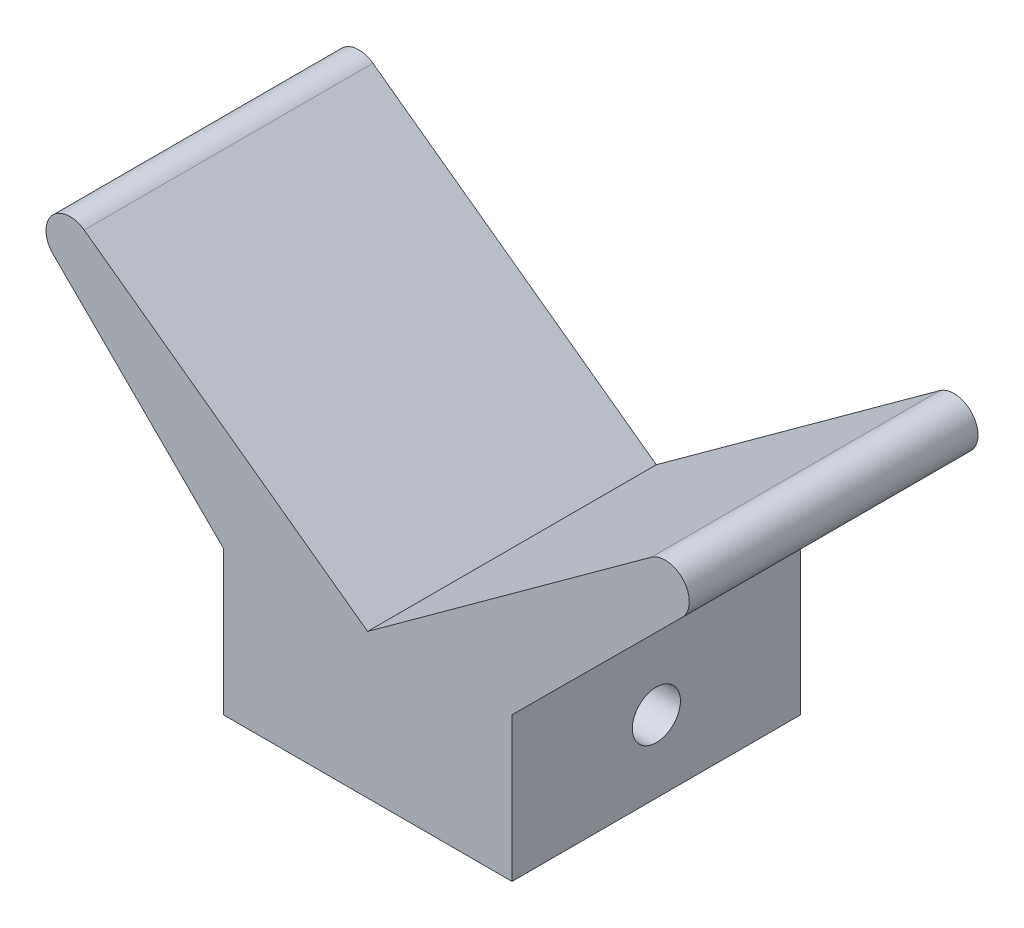
SolidWorks part; units mm, degrees
ref_plane "Front Plane" through (0, 0, 0) normal (0, 0, 1) x (1, 0, 0)
ref_plane "Top Plane" through (0, 0, 0) normal (0, 1, 0) x (1, 0, 0)
ref_plane "Right Plane" through (0, 0, 0) normal (1, 0, 0) x (0, 0, -1)
sketch "Sketch1" plane through (0, 0, 0) normal (0, 0, 1) x (1, 0, 0)
  line L0 (-38.1, 0) -> (38.1, 0)
  line L1 (38.1, 0) -> (38.1, 38.1)
  line L2 (38.1, 38.1) -> (83.0182, 82.8121)
  line L3 (74.806, 92.4498) -> (0, 38.1)
  line L4 (0, 0) -> (0, 38.1) construction
  line L5 (-74.806, 92.4498) -> (0, 38.1)
  line L6 (-38.1, 38.1) -> (-83.0182, 82.8121)
  line L7 (-38.1, 0) -> (-38.1, 38.1)
  arc A0 (83.0182, 82.8121) -> (74.806, 92.4498) centre (78.5385, 87.3125) ccw
  arc A1 (-83.0182, 82.8121) -> (-74.806, 92.4498) centre (-78.5385, 87.3125) cw
  point P13 (0, 0)
  point P14 (0, 0)
  dimension "D1" = 76.2
  dimension "D5" = 6.35
  dimension "D2" = 38.1
  dimension "D3" = 87.3125
  dimension "D4" = 108
extrude "Boss-Extrude1" add sketch "Sketch1" along normal blind 76.2
sketch "Sketch2" plane through (38.1, 0, 0) normal (1, 0, 0) x (0, 0, -1)
  line L2 (-76.2, 0) -> (0, 0) construction
  line L3 (-76.2, 0) -> (-76.2, 38.1) construction
  circle A0 centre (-38.1, 19.05) radius 6.35
  point P2 (0, 0)
  point P5 (0, 0)
  point P6 (0, 0)
  dimension "D1" = 12.7
  dimension "D2" = 19.05
  dimension "D3" = 38.1
extrude "Cut-Extrude1" cut sketch "Sketch2" against normal through all
